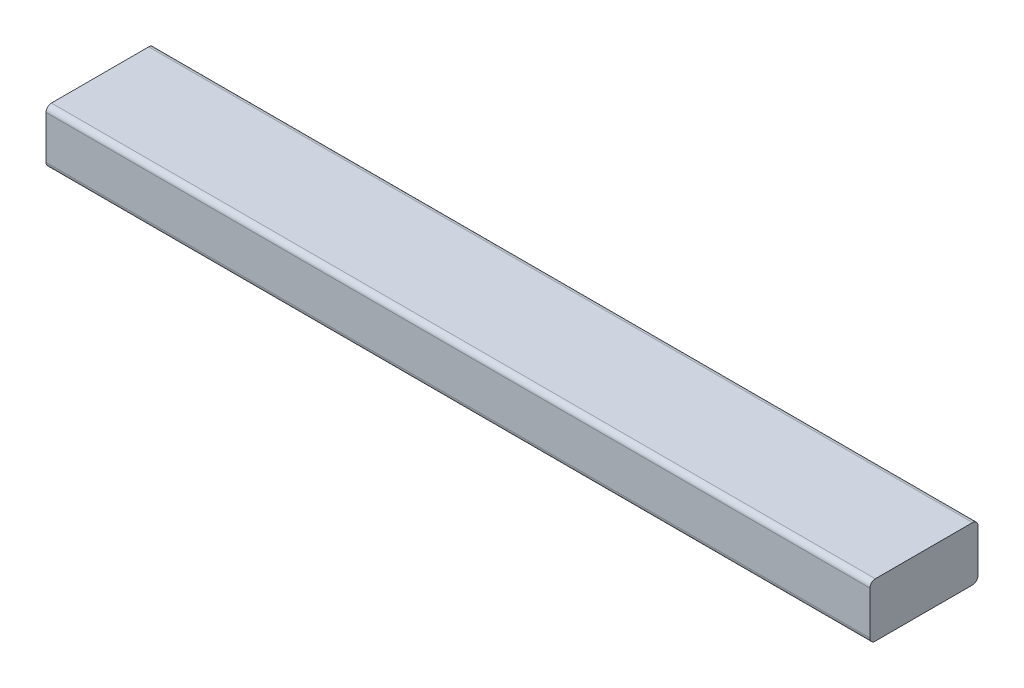
SolidWorks part; units mm, degrees
material "Balsa"
ref_plane "Front Plane" through (0, 0, 0) normal (0, 0, 1) x (1, 0, 0)
ref_plane "Top Plane" through (0, 0, 0) normal (0, 1, 0) x (1, 0, 0)
ref_plane "Right Plane" through (0, 0, 0) normal (1, 0, 0) x (0, 0, -1)
sketch "Sketch1" plane through (0, -12.7, 0) normal (0, -1, 0) x (-1, 0, 0)
  line L0 (-1812.7, 275) -> (-1812.7, -275) construction
  line L1 (-2587.3, 160.7) -> (-1812.7, 160.7)
  line L2 (-2587.3, 160.7) -> (-2587.3, 262.3)
  line L3 (-2587.3, 262.3) -> (-1812.7, 262.3)
  line L4 (-1812.7, 160.7) -> (-1812.7, 262.3)
  line L5 (-2588.0603, 262.3) -> (-1811.9397, 262.3) construction
  line L6 (-2587.3, -275) -> (-2587.3, 275) construction
  dimension "D1" = 101.6
extrude "Boss-Extrude1" add sketch "Sketch1" against normal blind 50.8
fillet "Fillet1" radius 5.08 4 edges at (2200, -12.7, -262.3) (2200, -12.7, -160.7) (2200, 38.1, -160.7) (2200, 38.1, -262.3)
